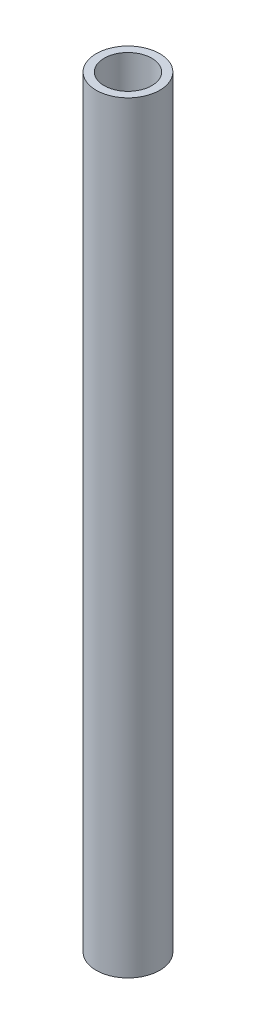
SolidWorks part; units mm, degrees
material "Hexcel AS4C (3000 Filaments)"
ref_plane "Front" through (0, 0, 0) normal (0, 0, 1) x (1, 0, 0)
ref_plane "Top" through (0, 0, 0) normal (0, 1, 0) x (1, 0, 0)
ref_plane "Right" through (0, 0, 0) normal (1, 0, 0) x (0, 0, -1)
sketch "Sketch1" plane through (0, 0, 0) normal (0, 1, 0) x (1, 0, 0)
  circle A0 centre (0, 0) radius 3.75
  circle A1 centre (0, 0) radius 5
  dimension "D1" = 10
  dimension "D2" = 7.5
extrude "Boss-Extrude1" add sketch "Sketch1" along normal blind 120
